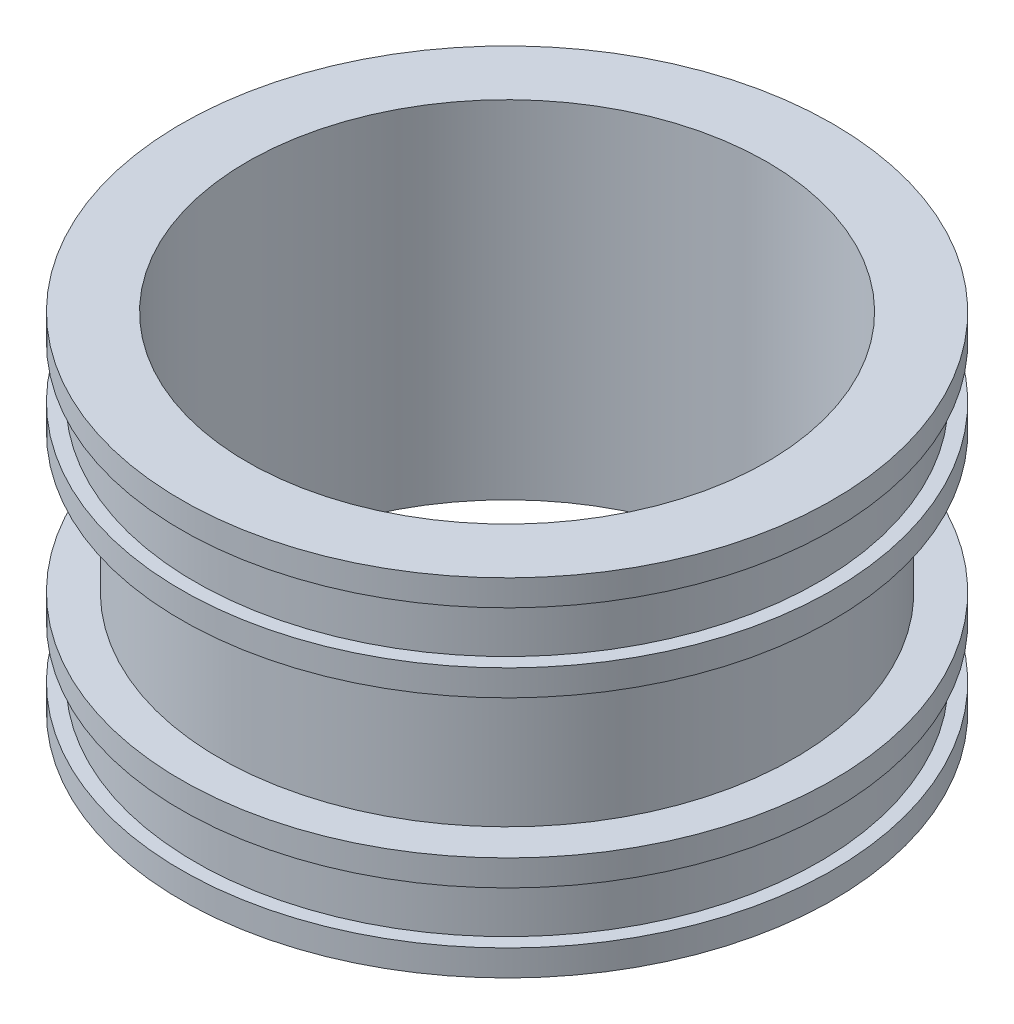
SolidWorks part; units mm, degrees
material "AISI 1020"
ref_plane "Plano frontal" through (0, 0, 0) normal (0, 0, 1) x (1, 0, 0)
ref_plane "Plano superior" through (0, 0, 0) normal (0, 1, 0) x (1, 0, 0)
ref_plane "Plano direito" through (0, 0, 0) normal (1, 0, 0) x (0, 0, -1)
sketch "Esboço1" plane through (0, 0, 0) normal (0, 0, 1) x (1, 0, 0)
  line L0 (0, 0) -> (0, 327.1613) construction
  line L1 (0, 0) -> (502.3995, 0) construction
  line L2 (75, 100) -> (94, 100)
  line L3 (94, 100) -> (94, 92.5)
  line L4 (94, 70) -> (83, 70)
  line L5 (83, 70) -> (83, 30)
  line L6 (83, 30) -> (94, 30)
  line L7 (94, 30) -> (94, 22.5)
  line L8 (94, 0) -> (75, 0)
  line L9 (75, 0) -> (75, 100)
  line L10 (94, 92.5) -> (90, 92.5)
  line L11 (90, 92.5) -> (90, 77.5)
  line L12 (90, 77.5) -> (94, 77.5)
  line L13 (75, 50) -> (94, 50) construction
  line L14 (94, 77.5) -> (94, 70)
  line L15 (90, 22.5) -> (94, 22.5)
  line L16 (90, 7.5) -> (90, 22.5)
  line L17 (94, 7.5) -> (90, 7.5)
  line L18 (94, 7.5) -> (94, 0)
  point P22 (83, 50)
  dimension "D1" = 150
  dimension "D2" = 4
  dimension "D3" = 15
  dimension "D4" = 30
  dimension "250" = 188
  dimension "D6" = 8
  dimension "D7" = 100
revolve "Revolução1" add sketch "Esboço1" angle 360 about L0
